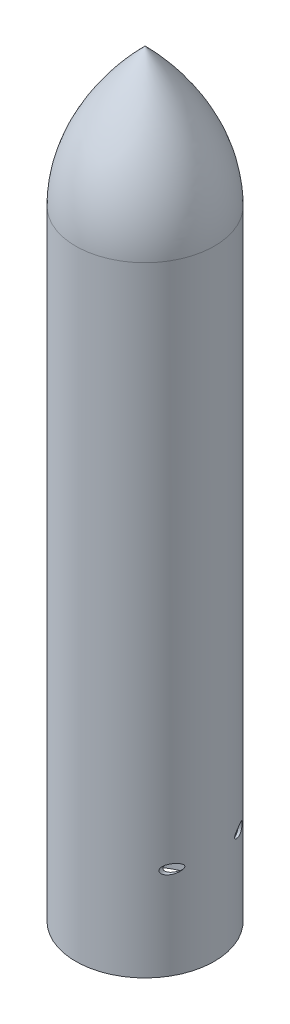
SolidWorks part; units mm, degrees
ref_plane "Front Plane" through (0, 0, 0) normal (0, 0, 1) x (1, 0, 0)
ref_plane "Top Plane" through (0, 0, 0) normal (0, 1, 0) x (1, 0, 0)
ref_plane "Right Plane" through (0, 0, 0) normal (1, 0, 0) x (0, 0, -1)
sketch "Sketch1" plane through (0, 0, 0) normal (0, 0, 1) x (1, 0, 0)
  line L0 (0, 1640) -> (-150, 1490) construction
  line L2 (0, 0) -> (0, 1640) construction
  line L4 (-150, 0) -> (-150, 1340)
  line L5 (-150, 1490) -> (-150, 1340) construction
  line L6 (-150, 1340) -> (0, 1340) construction
  line L7 (-75, 1340) -> (-75, 1640) construction
  line L8 (-145, 5) -> (-145, 1340)
  line L11 (-5, 1627.8031) -> (0, 1632.9527)
  line L12 (-5, 5) -> (-5, 1627.8031) construction
  line L14 (0, 1632.9527) -> (0, 1640)
  line L16 (-145, 5) -> (-145, 0)
  line L17 (-5, 5) -> (-145, 5) construction
  line L18 (0, 0) -> (-150, 0) construction
  line L19 (-145, 0) -> (-150, 0)
  spline S0 degree 2 poles (0, 1640) (-150, 1490) (-150, 1340) knots 0 0 0 1 1 1
  spline S1 degree 1 poles (-5, 1627.8031) (-145, 1340) knots 0 0 1 1 construction
  spline S2 degree 2 poles (-5, 1627.8031) (-57.6942, 1573.5116) (-112.3472, 1483.4265) (-145.0164, 1393.6706) (-145, 1340) knots 0.029046 0.029046 0.029046 0.393154 0.635892 1 1 1
  point P11 (-75, 1490)
  dimension "D1" = 1640
  dimension "D2" = 150
  dimension "D3" = 300
  dimension "D4" = 5
revolve "Revolve1" add sketch "Sketch1" angle 360 about L2
sketch "Sketch2" plane through (0, 0, 0) normal (0, 0, 1) x (1, 0, 0)
  line L0 (-150, 200) -> (150, 200) construction
  line L1 (-150, 1340) -> (-150, 0) construction
  line L2 (-150, 0) -> (150, 0) construction
  line L3 (0, 0) -> (0, 200) construction
  circle A0 centre (130, 200) radius 10
  point P10 (111.9095, 200)
  dimension "D2" = 20
  dimension "D3" = 20
  dimension "D1" = 200
extrude "Cut-Extrude1" cut sketch "Sketch2" along normal through all and the other way through all
mirror "Mirror1" about plane through (0, 0, 0) normal (1, 0, 0) of "Cut-Extrude1"
